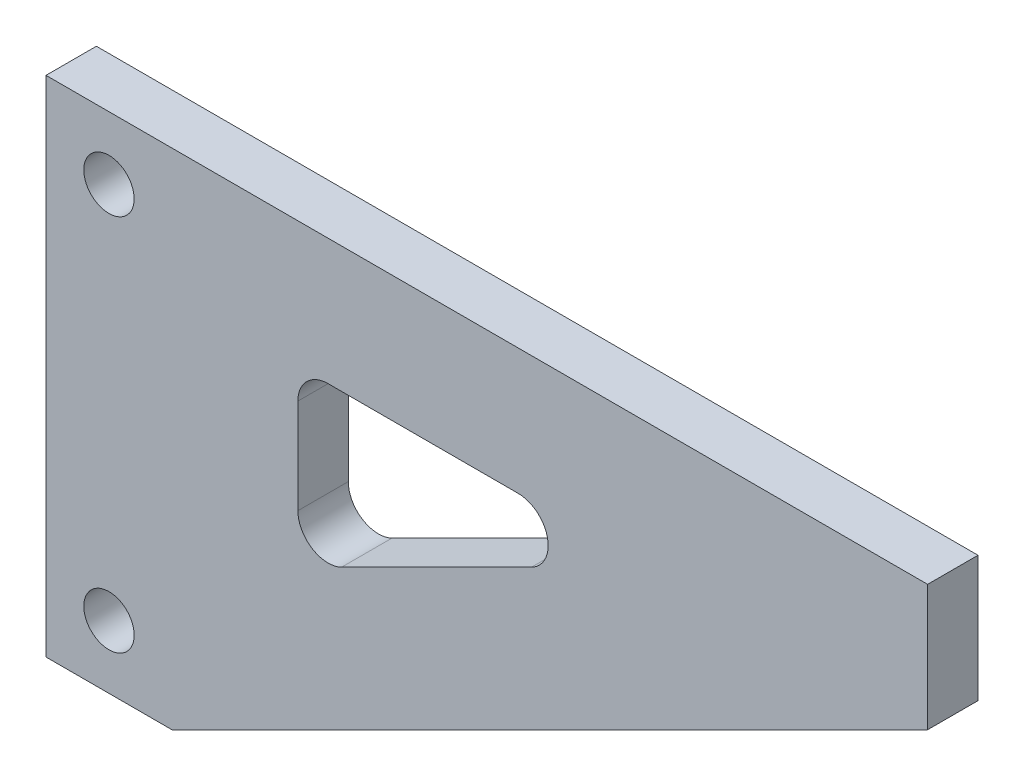
SolidWorks part; units mm, degrees
ref_plane "Plane1" through (0, 0, 0) normal (0, 0, 1) x (1, 0, 0)
ref_plane "Plane2" through (0, 0, 0) normal (0, 1, 0) x (1, 0, 0)
ref_plane "Plane3" through (0, 0, 0) normal (1, 0, 0) x (0, 0, -1)
other "Configuration Table"
sketch "Sketch1" plane through (0, 0, 0) normal (0, 0, 1) x (1, 0, 0)
  line L0 (0, 0) -> (25, 0)
  line L1 (0, 0) -> (0, 100)
  line L2 (0, 100) -> (175, 100)
  line L3 (175, 100) -> (175, 75)
  line L4 (175, 75) -> (25, 0)
  line L5 (50, 50.1591) -> (50, 69)
  line L6 (56, 75) -> (93.6819, 75)
  line L7 (96.3652, 63.6334) -> (58.6833, 44.7925)
  circle A0 centre (12.5, 12.5) radius 5
  circle A1 centre (12.5, 87.5) radius 5
  arc A2 (96.3652, 63.6334) -> (93.6819, 75) centre (93.6819, 69) ccw
  arc A3 (50, 50.1591) -> (58.6833, 44.7925) centre (56, 50.1591) ccw
  arc A4 (56, 75) -> (50, 69) centre (56, 69) ccw
  dimension "D5" = 10
  dimension "D6" = 10
  dimension "D14" = 6
  dimension "D1" = 25
  dimension "D2" = 100
  dimension "D3" = 175
  dimension "D4" = 25
  dimension "D7" = 12.5
  dimension "D8" = 12.5
  dimension "D9" = 12.5
  dimension "D10" = 12.5
  dimension "D11" = 25
  dimension "D12" = 25
  dimension "D13" = 50
extrude "Base-Extrude" add sketch "Sketch1" along normal blind 10
